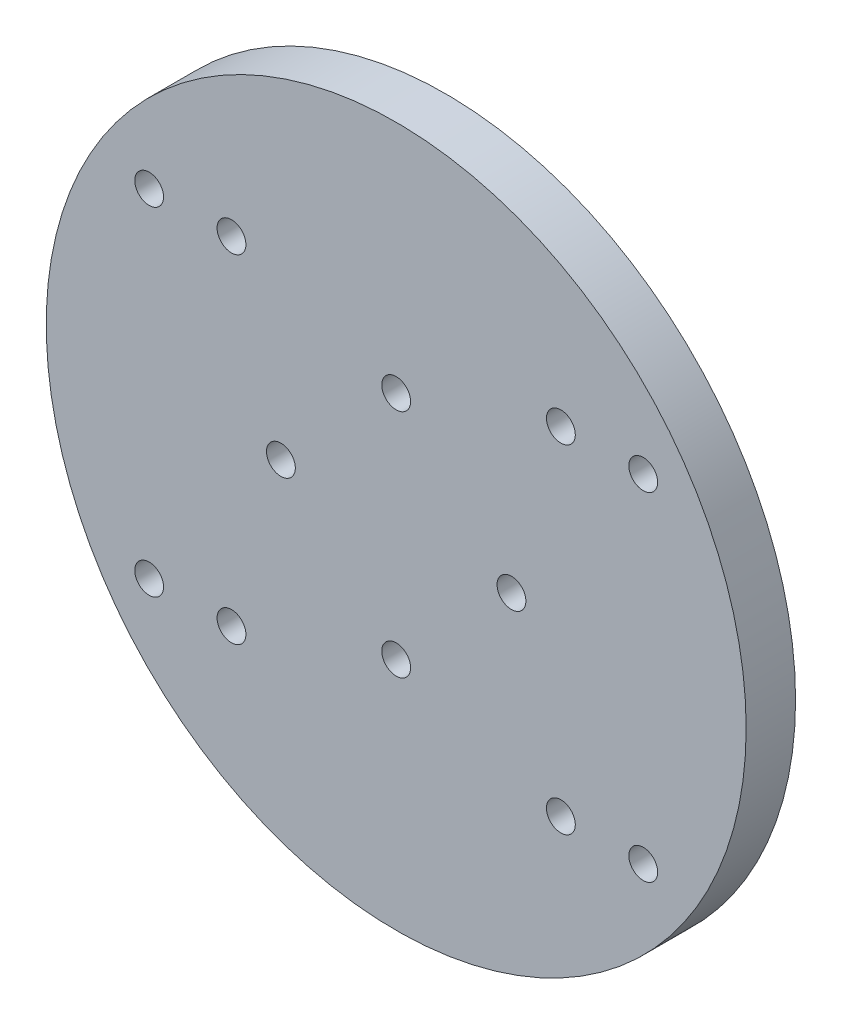
SolidWorks part; units mm, degrees
ref_plane "Front Plane" through (0, 0, 0) normal (0, 0, 1) x (1, 0, 0)
ref_plane "Top Plane" through (0, 0, 0) normal (0, 1, 0) x (1, 0, 0)
ref_plane "Right Plane" through (0, 0, 0) normal (1, 0, 0) x (0, 0, -1)
sketch "Sketch1" plane through (0, 0, 0) normal (0, 0, 1) x (1, 0, 0)
  circle A0 centre (0, 0) radius 42.5
  dimension "D1" = 85
extrude "Boss-Extrude1" add sketch "Sketch1" along normal blind 6
sketch "Sketch2" plane through (0, 0, 0) normal (0, 0, -1) x (-1, 0, 0)
  circle A0 centre (0, 0) radius 22
  dimension "D1" = 44
extrude "Boss-Extrude2" add sketch "Sketch2" along normal blind 6
sketch "Sketch3" plane through (0, 0, -6) normal (0, 0, -1) x (-1, 0, 0)
  circle A0 centre (0, 0) radius 20.1
  dimension "D1" = 40.2
extrude "Boss-Extrude3" add sketch "Sketch3" along normal blind 4.7
sketch "Sketch4" plane through (0, 0, -10.7) normal (0, 0, -1) x (-1, 0, 0)
  circle A0 centre (0, 0) radius 18.1
  dimension "D1" = 36.2
extrude "Cut-Extrude1" cut sketch "Sketch4" against normal blind 11
sketch "Sketch5" plane through (0, 0, 0.3) normal (0, 0, -1) x (-1, 0, 0)
  circle A4 centre (14, 0) radius 1.75
  circle A5 centre (0, -14) radius 1.75
  circle A6 centre (-14, 0) radius 1.75
  circle A7 centre (0, 14) radius 1.75
  point P11 (0, 0)
  point P12 (0, 0)
  dimension "D1" = 3.5
  dimension "D2" = 14
  dimension "D3" = 4
extrude "Cut-Extrude2" cut sketch "Sketch5" against normal through all
sketch "Sketch6" plane through (0, 0, 0.3) normal (0, 0, -1) x (-1, 0, 0)
  line L0 (20, -20.5) -> (20, 20.5)
  line L1 (0, 0) -> (0, -39.3338)
  circle A0 centre (20, -20.5) radius 1.75
  circle A1 centre (-20, 20.5) radius 1.75
  circle A2 centre (-20, -20.5) radius 1.75
  circle A3 centre (20, 20.5) radius 1.75
  point P3 (20, 0)
  dimension "D3" = 3.5
  dimension "D1" = 41
  dimension "D2" = 20
  dimension "D5" = 41
  dimension "D4" = 2
extrude "Cut-Extrude3" cut sketch "Sketch6" against normal through all both and the other way through all contours A2 | A1 | A3 | A0
sketch "Sketch7" plane through (0, 0, 0) normal (0, 0, 1) x (1, 0, 0)
  circle A0 centre (20, 20.5) radius 2.9
  circle A1 centre (-20, 20.5) radius 2.9
  circle A2 centre (-20, -20.5) radius 2.9
  circle A3 centre (20, -20.5) radius 2.9
  dimension "D1" = 5.8
  dimension "D2" = 5.8
  dimension "D3" = 5.8
  dimension "D4" = 5.8
extrude "Cut-Extrude5" cut sketch "Sketch7" along normal blind 3.3
sketch "Sketch8" plane through (0, 0, 6) normal (0, 0, 1) x (1, 0, 0)
  line L0 (0, 0) -> (0, 6.8455)
  circle A2 centre (0, 0) radius 42.5 construction
  circle A4 centre (-30, -20.5) radius 1.75
  circle A6 centre (-30, 20.5) radius 1.75
  circle A7 centre (30, 20.5) radius 1.75
  circle A8 centre (30, -20.5) radius 1.75
  circle A9 centre (-20, -20.5) radius 1.75 construction
  point P2 (-31.0838, -28.9836)
  point P3 (31.0838, -28.9836)
  dimension "D2" = 10
  dimension "D1" = 2
  dimension "3,3" = 3.5
extrude "Cut-Extrude6" cut sketch "Sketch8" against normal blind 10 contours A4 | A6 | A7 | A8
sketch "Sketch9" plane through (0, 0, 0) normal (0, 0, -1) x (-1, 0, 0)
  line L0 (0, 0) -> (0, 8.3554)
  circle A0 centre (-30, -20.5) radius 2.9
  circle A1 centre (-30, 20.5) radius 2.9
  circle A2 centre (30, -20.5) radius 2.9
  circle A3 centre (30, 20.5) radius 2.9
  dimension "D1" = 5.8
  dimension "D2" = 2
extrude "Cut-Extrude7" cut sketch "Sketch9" against normal blind 3.3 contours A1 | A0 | A2 | A3
